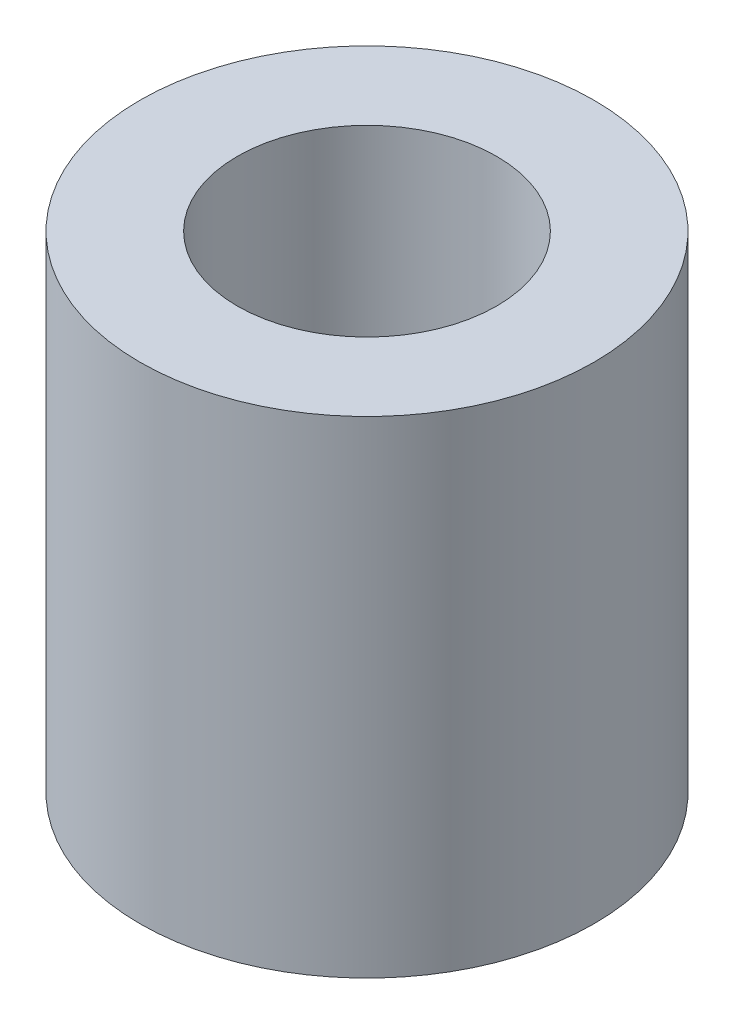
SolidWorks part; units mm, degrees
ref_plane "Front Plane" through (0, 0, 0) normal (0, 0, 1) x (1, 0, 0)
ref_plane "Top Plane" through (0, 0, 0) normal (0, 1, 0) x (1, 0, 0)
ref_plane "Right Plane" through (0, 0, 0) normal (1, 0, 0) x (0, 0, -1)
sketch "Sketch1" plane through (0, 0, 0) normal (0, 1, 0) x (1, 0, 0)
  circle A0 centre (0, 0) radius 7
  circle A1 centre (0, 0) radius 4
  dimension "D1" = 14
  dimension "D2" = 8
extrude "Boss-Extrude1" add sketch "Sketch1" along normal blind 15
